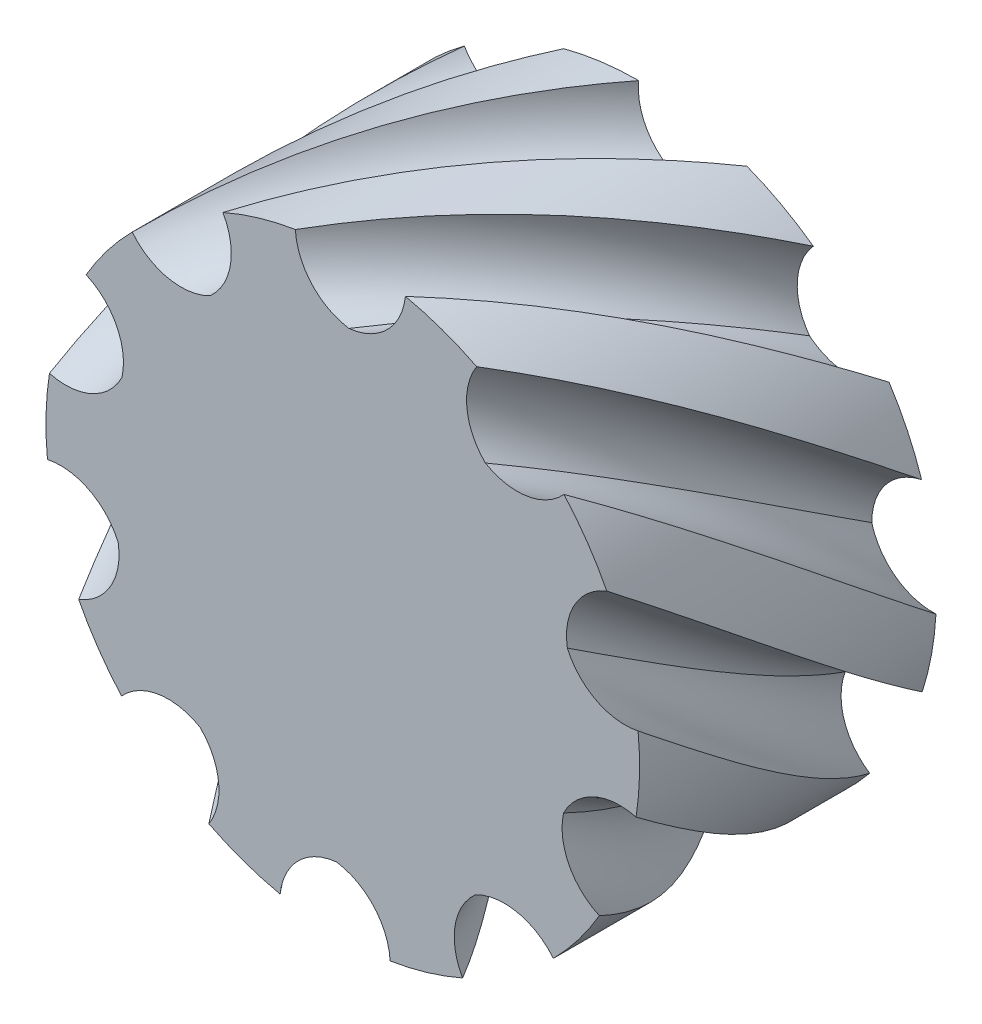
SolidWorks part; units mm, degrees
ref_plane "Front Plane" through (0, 0, 0) normal (0, 0, 1) x (1, 0, 0)
ref_plane "Top Plane" through (0, 0, 0) normal (0, 1, 0) x (1, 0, 0)
ref_plane "Right Plane" through (0, 0, 0) normal (1, 0, 0) x (0, 0, -1)
sketch "Sketch1" plane through (0, 0, 0) normal (0, 0, 1) x (1, 0, 0)
  circle A0 centre (0, 0) radius 4 construction
  circle A1 centre (0, 0) radius 4.8 construction
  circle A2 centre (0, 0) radius 5
extrude "Extrude1" add sketch "Sketch1" along normal blind 5
sketch "Sketch2" plane through (0, 0, 5) normal (0, 0, 1) x (1, 0, 0)
  line L0 (0, 5) -> (0.9972, 4.637) construction
  line L1 (1.0553, 4.8874) -> (1.5875, 6.35)
  line L2 (1.5875, 6.35) -> (-1.5875, 6.35)
  line L3 (0.6677, 12.7401) -> (0, 0) construction
  line L4 (0, 0) -> (9.525, 0) construction
  line L5 (0, 5) -> (3.7514, 5) construction
  line L6 (-1.5875, 6.35) -> (-0.798, 4.9359)
  circle A0 centre (0, 0) radius 5 construction
  circle A1 centre (0, 0) radius 4.8 construction
  circle A2 centre (0, 0) radius 4 construction
  circle A3 centre (0, 5) radius 1.0612 construction
  circle A4 centre (0.1994, 4.9274) radius 0.849 construction
  circle A5 centre (0.2617, 4.9931) radius 1.0612 construction
  arc A6 (0.1033, 3.9438) -> (1.0553, 4.8874) centre (0, 5) ccw
  arc A7 (0.1033, 3.9438) -> (-0.798, 4.9359) centre (0.2617, 4.9931) cw
  point P5 (0, 5)
  point P8 (0.9972, 4.637)
  point P9 (0.1994, 4.9274)
  point P14 (0.2617, 4.9931)
  point P19 (0.3163, 3.9875)
  point P20 (-0.1084, 3.9985)
  point P21 (0.1033, 3.9438)
  dimension "D1" = 10
  dimension "D2" = 9.6
  dimension "D3" = 8
  dimension "D4" = 20
  dimension "D5" = 0.849
  dimension "D6" = 2.1225
  dimension "D7" = 87
  dimension "RO2" = 2.1225
sketch "Sketch4" plane through (0, 0, 5) normal (0, 0, 1) x (1, 0, 0)
  circle A0 centre (0, 0) radius 5
curve "Helix/Spiral1" pitch 40 height 8 turns 0.2
sweep "Cut-Sweep1" cut profiles "Sketch2" path "Helix/Spiral1"
pattern_circular "CirPattern1" count 10 over 360 of "Cut-Sweep1"
equation "\"D6@Sketch2\" = \"RO2\""
